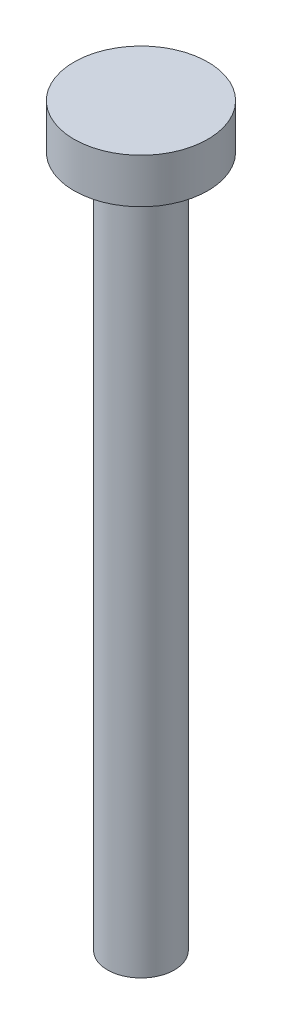
SolidWorks part; units mm, degrees
ref_plane "Front Plane" through (0, 0, 0) normal (0, 0, 1) x (1, 0, 0)
ref_plane "Top Plane" through (0, 0, 0) normal (0, 1, 0) x (1, 0, 0)
ref_plane "Right Plane" through (0, 0, 0) normal (1, 0, 0) x (0, 0, -1)
sketch "Sketch1" plane through (0, 0, 0) normal (0, 1, 0) x (1, 0, 0)
  circle A0 centre (0, 0) radius 1.5
extrude "Boss-Extrude1" add sketch "Sketch1" along normal blind 31
sketch "Sketch2" plane through (0, 31, 0) normal (0, 1, 0) x (1, 0, 0)
  circle A0 centre (0, 0) radius 3
extrude "Boss-Extrude2" add sketch "Sketch2" along normal blind 2
fillet "Fillet1" radius 1 1 edges at (0, 31, 1.5)
